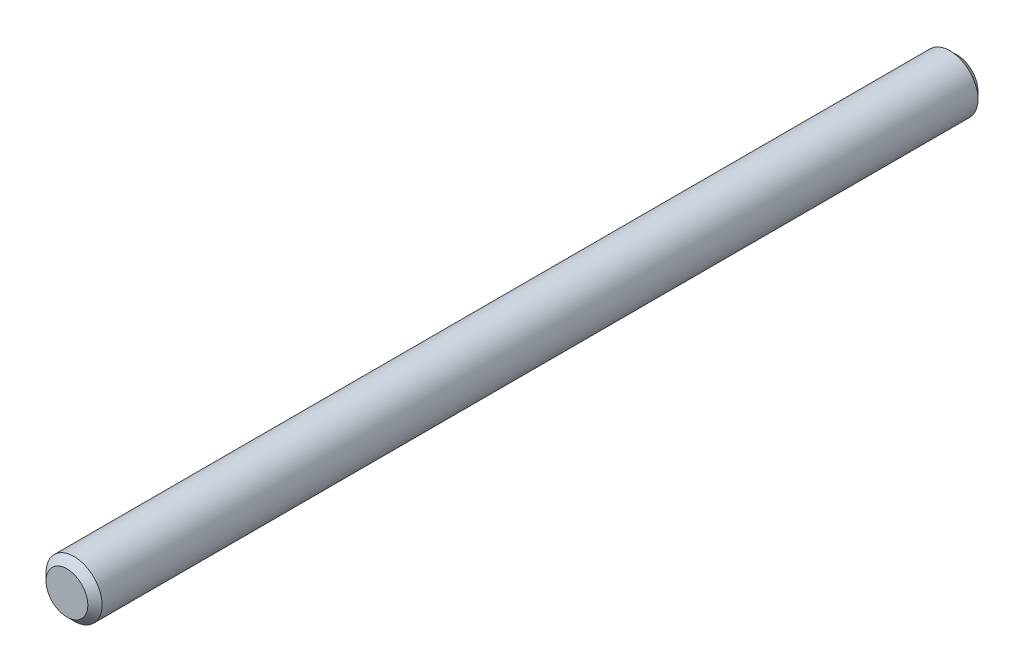
SolidWorks part; units mm, degrees
ref_plane "Front Plane" through (0, 0, 0) normal (0, 0, 1) x (1, 0, 0)
ref_plane "Top Plane" through (0, 0, 0) normal (0, 1, 0) x (1, 0, 0)
ref_plane "Right Plane" through (0, 0, 0) normal (1, 0, 0) x (0, 0, -1)
sketch "Sketch1" plane through (0, 0, 0) normal (0, 0, 1) x (1, 0, 0)
  circle A0 centre (0, 0) radius 2
  dimension "D1" = 4
extrude "Boss-Extrude1" add sketch "Sketch1" along normal blind 63.5
chamfer "Chamfer1" distance 0.508 angle 45 2 edges at (2, 0, 0) (2, 0, 63.5)
